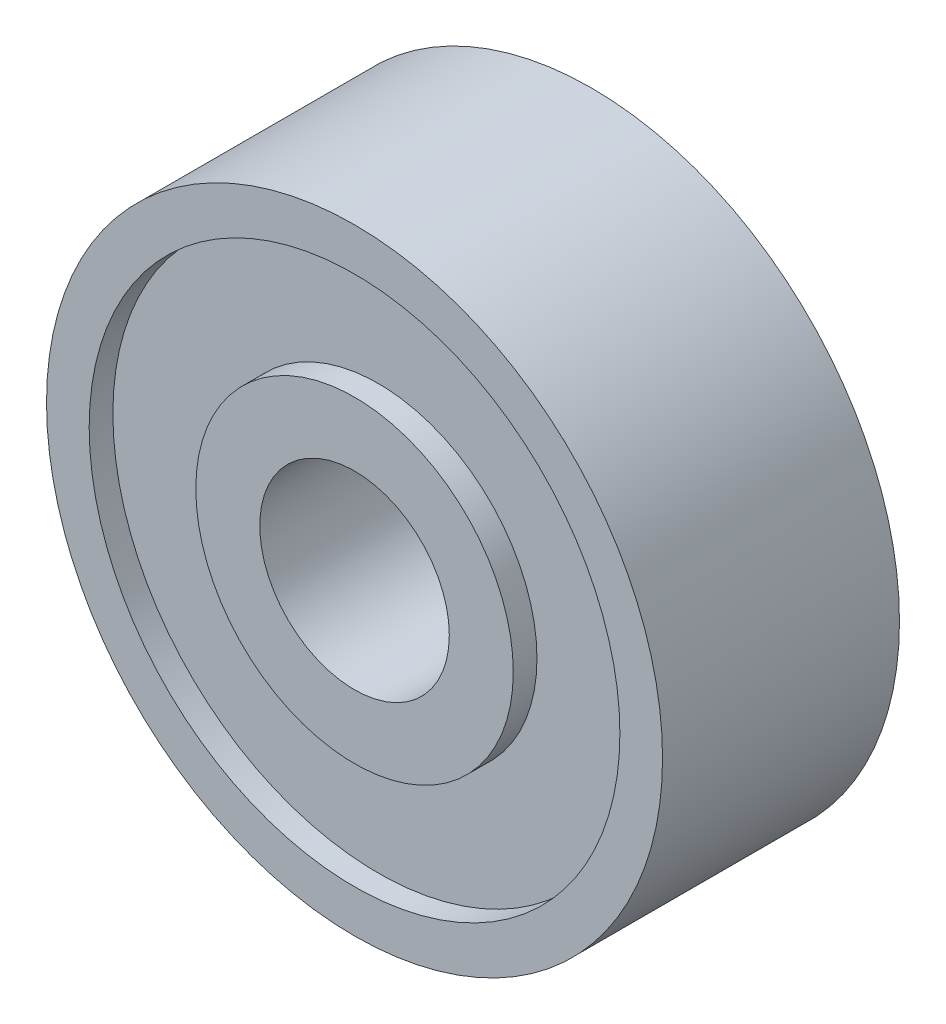
SolidWorks part; units mm, degrees
ref_plane "前基準面" through (0, 0, 0) normal (0, 0, 1) x (1, 0, 0)
ref_plane "上基準面" through (0, 0, 0) normal (0, 1, 0) x (1, 0, 0)
ref_plane "右基準面" through (0, 0, 0) normal (1, 0, 0) x (0, 0, -1)
sketch "草圖1" plane through (0, 0, 0) normal (0, 0, 1) x (1, 0, 0)
  circle A0 centre (0, 0) radius 6.5
  dimension "D1" = 13
extrude "填料-伸長1" add sketch "草圖1" along normal blind 5
sketch "草圖2" plane through (0, 0, 5) normal (0, 0, 1) x (1, 0, 0)
  circle A0 centre (0, 0) radius 2
  dimension "D1" = 4
extrude "除料-伸長1" cut sketch "草圖2" against normal through all
sketch "草圖3" plane through (0, 0, 5) normal (0, 0, 1) x (1, 0, 0)
  circle A0 centre (0, 0) radius 3.35
  circle A1 centre (0, 0) radius 5.6
  dimension "D1" = 6.7
  dimension "D2" = 11.2
extrude "除料-伸長2" cut sketch "草圖3" against normal blind 0.5
sketch "草圖4" plane through (0, 0, 0) normal (0, 0, -1) x (-1, 0, 0)
  circle A0 centre (0, 0) radius 3.35
  circle A1 centre (0, 0) radius 5.6
  dimension "D1" = 11.2
  dimension "D2" = 6.7
extrude "除料-伸長3" cut sketch "草圖4" against normal blind 0.5
